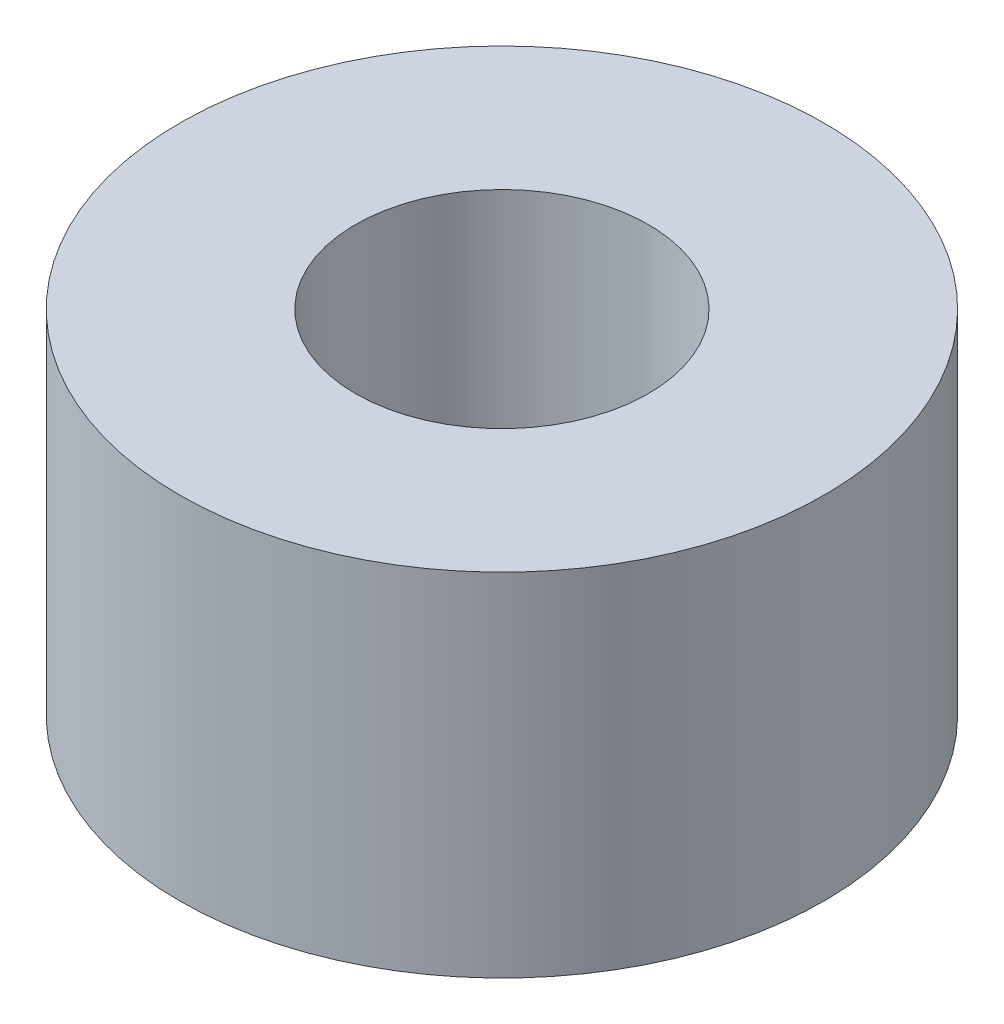
SolidWorks part; units mm, degrees
ref_plane "Front Plane" through (0, 0, 0) normal (0, 0, 1) x (1, 0, 0)
ref_plane "Top Plane" through (0, 0, 0) normal (0, 1, 0) x (1, 0, 0)
ref_plane "Right Plane" through (0, 0, 0) normal (1, 0, 0) x (0, 0, -1)
sketch "Sketch1" plane through (0, 0, 0) normal (0, 1, 0) x (1, 0, 0)
  circle A0 centre (0, 0) radius 2.5
  circle A1 centre (0, 0) radius 5.5
  dimension "D1" = 5
  dimension "D2" = 11
extrude "Boss-Extrude1" add sketch "Sketch1" along normal blind 6
